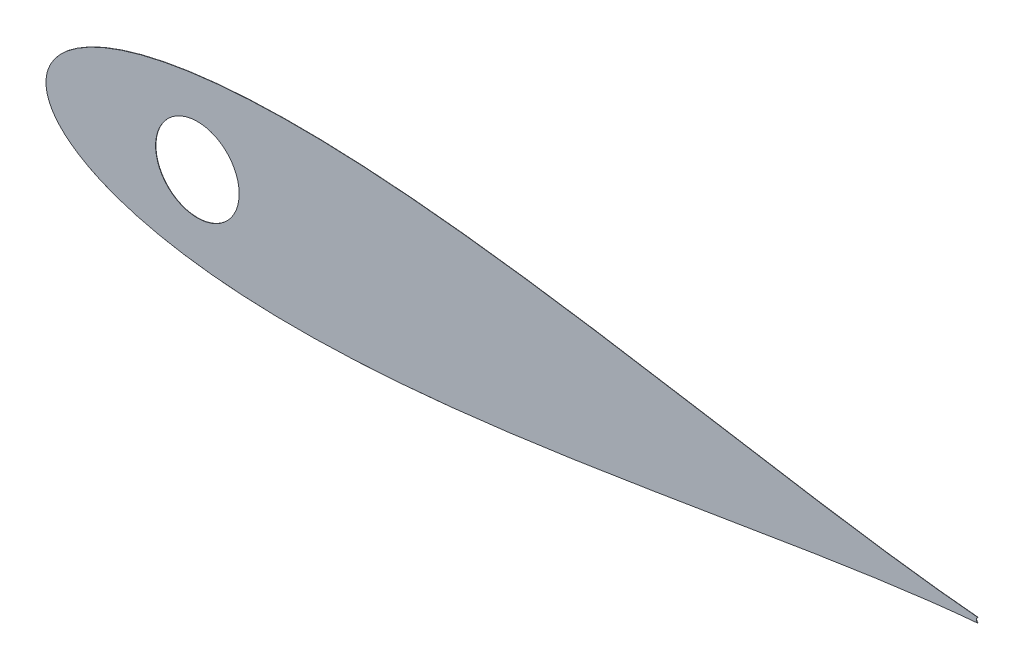
SolidWorks part; units mm, degrees
material "Custom Plastic"
ref_plane "Front Plane" through (0, 0, 0) normal (0, 0, 1) x (1, 0, 0)
ref_plane "Top Plane" through (0, 0, 0) normal (0, 1, 0) x (1, 0, 0)
ref_plane "Right Plane" through (0, 0, 0) normal (1, 0, 0) x (0, 0, -1)
sketch "Model" plane through (0, 0, 0) normal (0, 0, 1) x (1, 0, 0)
  line L0 (632.1834, 567.3179) -> (632.1834, 572.0669)
  line L1 (632.6583, 567.3179) -> (632.1834, 567.3179)
  line L2 (632.6583, 572.6096) -> (632.6583, 567.3179)
  line L3 (631.6799, 572.6096) -> (632.6583, 572.6096)
  line L4 (631.3693, 572.0669) -> (631.6799, 572.6096)
  line L5 (632.1834, 572.0669) -> (631.3693, 572.0669)
  line L6 (629.6733, 570.71) -> (628.7595, 570.71)
  line L7 (629.6733, 571.0492) -> (629.6733, 570.71)
  line L8 (628.8104, 571.0492) -> (629.6733, 571.0492)
  line L9 (629.0648, 572.7453) -> (628.8104, 571.0492)
  line L10 (628.6556, 572.7453) -> (629.0648, 572.7453)
  line L11 (628.4012, 571.0492) -> (628.6556, 572.7453)
  line L12 (627.3179, 571.0492) -> (628.4012, 571.0492)
  line L13 (627.5723, 572.7453) -> (627.3179, 571.0492)
  line L14 (627.1631, 572.7453) -> (627.5723, 572.7453)
  line L15 (626.9087, 571.0492) -> (627.1631, 572.7453)
  line L16 (625.8741, 571.0492) -> (626.9087, 571.0492)
  line L17 (625.8741, 570.71) -> (625.8741, 571.0492)
  line L18 (626.8578, 570.71) -> (625.8741, 570.71)
  line L19 (626.6744, 569.4889) -> (626.8578, 570.71)
  line L20 (625.7384, 569.4889) -> (626.6744, 569.4889)
  line L21 (625.7384, 569.1497) -> (625.7384, 569.4889)
  line L22 (626.6236, 569.1497) -> (625.7384, 569.1497)
  line L23 (626.349, 567.3179) -> (626.6236, 569.1497)
  line L24 (626.7592, 567.3179) -> (626.349, 567.3179)
  line L25 (627.0338, 569.1497) -> (626.7592, 567.3179)
  line L26 (628.1161, 569.1497) -> (627.0338, 569.1497)
  line L27 (627.8415, 567.3179) -> (628.1161, 569.1497)
  line L28 (628.2518, 567.3179) -> (627.8415, 567.3179)
  line L29 (628.5263, 569.1497) -> (628.2518, 567.3179)
  line L30 (629.5376, 569.1497) -> (628.5263, 569.1497)
  line L31 (629.5376, 569.4889) -> (629.5376, 569.1497)
  line L32 (628.5772, 569.4889) -> (629.5376, 569.4889)
  line L33 (628.7595, 570.71) -> (628.5772, 569.4889)
  line L34 (627.267, 570.71) -> (627.0847, 569.4889)
  line L35 (628.3503, 570.71) -> (627.267, 570.71)
  line L36 (628.167, 569.4889) -> (628.3503, 570.71)
  line L37 (627.0847, 569.4889) -> (628.167, 569.4889)
  arc A0 (733.0945, 571.1452) -> (733.0926, 569.082) centre (733.7898, 570.113) ccw
  circle A1 centre (374.0091, 570.113) radius 10.1301
  circle A2 centre (607.3416, 570.113) radius 6.35
  circle A3 centre (567.9716, 570.113) radius 12.7
  circle A4 centre (518.2881, 570.113) radius 19.3008
  circle A5 centre (464.3241, 570.113) radius 23.3784
  circle A6 centre (410.4916, 570.1137) radius 17.272
  spline S0 degree 3 poles (733.0945, 571.1452) (731.0717, 571.3179) (726.7738, 571.7153) (719.931, 572.4271) (712.3349, 573.3017) (704.0224, 574.3433) (695.0324, 575.5531) (685.4036, 576.9284) (675.1779, 578.462) (664.3986, 580.143) (653.1109, 581.9565) (641.3614, 583.8836) (629.1982, 585.9022) (616.6704, 587.9868) (603.8283, 590.1092) (590.7233, 592.2384) (577.4078, 594.342) (563.9349, 596.3855) (550.3591, 598.3339) (536.7354, 600.1516) (523.1201, 601.8031) (509.5703, 603.2536) (496.1441, 604.4696) (482.9006, 605.4195) (469.9, 606.074) (457.2032, 606.4066) (444.8723, 606.3942) (432.9703, 606.0174) (421.5609, 605.2612) (410.7094, 604.1149) (400.482, 602.5731) (390.9469, 600.6353) (382.1748, 598.3081) (374.2396, 595.6051) (367.2206, 592.5504) (361.2031, 589.1843) (356.2769, 585.5753) (352.525, 581.8411) (349.9848, 578.1793) (348.5684, 574.8757) (347.9964, 572.2255) (347.8662, 570.1137) (347.9964, 568.0019) (348.5684, 565.3517) (349.9848, 562.0481) (352.525, 558.3863) (356.2769, 554.6521) (361.2031, 551.0431) (367.2206, 547.677) (374.2396, 544.6223) (382.1748, 541.9193) (390.9469, 539.5921) (400.482, 537.6543) (410.7094, 536.1125) (421.5609, 534.9662) (432.9703, 534.21) (444.8723, 533.8332) (457.2032, 533.8208) (469.9, 534.1534) (482.9006, 534.8078) (496.1441, 535.7578) (509.5703, 536.9738) (523.1201, 538.4243) (536.7354, 540.0758) (550.3591, 541.8935) (563.9349, 543.8419) (577.4078, 545.8854) (590.7233, 547.989) (603.8283, 550.1182) (616.6704, 552.2406) (629.1982, 554.3252) (641.3614, 556.3438) (653.1109, 558.2709) (664.3986, 560.0844) (675.1779, 561.7654) (685.4036, 563.299) (695.0324, 564.6743) (704.0224, 565.8841) (712.3349, 566.9257) (719.931, 567.8003) (726.7732, 568.5121) (731.0705, 568.9094) (733.0926, 569.082) knots 0.021301 0.021301 0.021301 0.021301 0.028553 0.036781 0.04592 0.055932 0.066773 0.078397 0.090755 0.103793 0.117456 0.131686 0.146422 0.1616 0.177156 0.193024 0.209135 0.225421 0.241812 0.258238 0.274629 0.290914 0.307025 0.322893 0.338448 0.353626 0.368361 0.38259 0.396253 0.40929 0.421647 0.43327 0.444109 0.454119 0.463255 0.471479 0.478755 0.485052 0.490344 0.49461 0.497833 0.5 0.502167 0.50539 0.509656 0.514948 0.521245 0.528521 0.536745 0.545881 0.555891 0.56673 0.578353 0.59071 0.603747 0.61741 0.631639 0.646374 0.661552 0.677107 0.692975 0.709086 0.725371 0.741762 0.758188 0.774579 0.790865 0.806976 0.822844 0.8384 0.853578 0.868314 0.882544 0.896207 0.909245 0.921603 0.933227 0.944068 0.95408 0.963219 0.971447 0.978697 0.978697 0.978697 0.978697
  spline S1 degree 3 poles (638.2213, 569.9616) (638.2203, 569.8807) (638.2184, 569.723) (638.2085, 569.4924) (638.1889, 569.2747) (638.1644, 569.0694) (638.1304, 568.8773) (638.0887, 568.6978) (638.0424, 568.53) (637.9852, 568.3754) (637.9226, 568.2319) (637.8544, 568.0978) (637.7815, 567.9721) (637.7019, 567.8557) (637.6172, 567.7478) (637.5254, 567.6502) (637.4291, 567.5608) (637.3272, 567.4812) (637.2208, 567.4115) (637.112, 567.3492) (636.9989, 567.2989) (636.8841, 567.2558) (636.766, 567.2228) (636.6447, 567.2001) (636.5208, 567.1841) (636.437, 567.1829) (636.3949, 567.1822) knots 0 0 0 0 0.065063 0.126773 0.185516 0.240765 0.29298 0.34225 0.388919 0.432776 0.474628 0.514775 0.553606 0.591426 0.628028 0.663804 0.698984 0.733591 0.767628 0.801208 0.834264 0.866981 0.89972 0.932702 0.966176 1 1 1 1
  spline S2 degree 3 poles (636.3949, 572.7453) (636.437, 572.7445) (636.5207, 572.7431) (636.6444, 572.729) (636.7653, 572.7056) (636.8828, 572.6724) (636.9979, 572.6313) (637.1097, 572.5798) (637.2188, 572.5198) (637.3237, 572.4493) (637.4253, 572.3707) (637.5212, 572.2819) (637.6115, 572.1837) (637.6971, 572.0772) (637.7758, 571.9603) (637.8508, 571.8352) (637.9179, 571.6995) (637.9825, 571.5556) (638.0383, 571.3995) (638.0886, 571.232) (638.1292, 571.0512) (638.163, 570.8581) (638.1893, 570.6518) (638.2084, 570.433) (638.2185, 570.2013) (638.2204, 570.0429) (638.2213, 569.9616) knots 0 0 0 0 0.033788 0.067194 0.099862 0.132567 0.165151 0.197913 0.231319 0.265083 0.299255 0.334399 0.369943 0.406284 0.444064 0.482998 0.523354 0.565537 0.609613 0.656391 0.705885 0.758325 0.813832 0.872795 0.934722 1 1 1 1
  spline S3 degree 3 poles (634.6257, 569.9616) (634.6262, 570.0465) (634.6272, 570.2112) (634.6379, 570.4513) (634.6557, 570.6765) (634.6801, 570.8869) (634.7098, 571.0824) (634.7494, 571.2627) (634.7945, 571.4285) (634.8467, 571.5804) (634.9057, 571.7203) (634.9698, 571.851) (635.0417, 571.9722) (635.1173, 572.0858) (635.1996, 572.1899) (635.2862, 572.2862) (635.3806, 572.3722) (635.4795, 572.4506) (635.5838, 572.5193) (635.6906, 572.5798) (635.8006, 572.6315) (635.9141, 572.6722) (636.0301, 572.7058) (636.149, 572.7287) (636.2709, 572.7432) (636.3532, 572.7446) (636.3949, 572.7453) knots 0 0 0 0 0.068595 0.133246 0.194313 0.251279 0.304513 0.354235 0.400481 0.443411 0.484015 0.523252 0.561042 0.5979 0.633518 0.668314 0.702496 0.736685 0.770293 0.803437 0.835913 0.86846 0.900847 0.933467 0.966258 1 1 1 1
  spline S4 degree 3 poles (636.3949, 567.1822) (636.3532, 567.1829) (636.2709, 567.1843) (636.1489, 567.1987) (636.0306, 567.2218) (635.9152, 567.2542) (635.8023, 567.2939) (635.6933, 567.3455) (635.587, 567.405) (635.4838, 567.4727) (635.3855, 567.5503) (635.2916, 567.6361) (635.2045, 567.7323) (635.1234, 567.8373) (635.0463, 567.9503) (634.9754, 568.0726) (634.9098, 568.2039) (634.8499, 568.345) (634.7968, 568.498) (634.7498, 568.6645) (634.7127, 568.8461) (634.681, 569.0413) (634.6554, 569.251) (634.638, 569.4752) (634.6272, 569.7138) (634.6262, 569.8775) (634.6257, 569.9616) knots 0 0 0 0 0.033787 0.066622 0.099285 0.131361 0.163585 0.196104 0.228902 0.262158 0.295991 0.330218 0.36506 0.400951 0.43762 0.475708 0.515381 0.556414 0.599765 0.646424 0.696431 0.749782 0.806573 0.867436 0.931887 1 1 1 1
  spline S5 degree 3 poles (637.5461, 568.6334) (637.562, 568.6806) (637.5944, 568.7765) (637.6362, 568.9252) (637.6691, 569.0813) (637.6986, 569.2437) (637.7188, 569.4137) (637.7351, 569.5907) (637.7447, 569.775) (637.7458, 569.9001) (637.7464, 569.9638) knots 0 0 0 0 0.110588 0.224542 0.342503 0.464324 0.590756 0.722227 0.858843 1 1 1 1
  spline S6 degree 3 poles (636.4108, 572.2025) (636.3523, 572.1995) (636.2351, 572.1933) (636.0621, 572.1499) (635.8962, 572.0743) (635.7643, 571.9912) (635.6632, 571.9121) (635.592, 571.8435) (635.5253, 571.7684) (635.4638, 571.6862) (635.4062, 571.5978) (635.3533, 571.5026) (635.3057, 571.4) (635.2617, 571.2902) (635.223, 571.1699) (635.1912, 571.0372) (635.1617, 570.8914) (635.1408, 570.7315) (635.1223, 570.5587) (635.1104, 570.3723) (635.1011, 570.1727) (635.1008, 570.0348) (635.1006, 569.9638) knots 0 0 0 0 0.060387 0.120883 0.182755 0.247811 0.281299 0.315088 0.349702 0.384857 0.420966 0.458511 0.497175 0.537602 0.580503 0.627468 0.678388 0.733983 0.793747 0.857714 0.926698 1 1 1 1
  spline S7 degree 3 poles (636.4108, 567.725) (636.4694, 567.7274) (636.5865, 567.7322) (636.7575, 567.7788) (636.9236, 567.849) (637.0537, 567.9321) (637.1527, 568.0112) (637.2236, 568.0787) (637.2888, 568.1542) (637.3505, 568.2357) (637.4071, 568.3247) (637.4586, 568.4208) (637.5056, 568.5243) (637.5324, 568.5965) (637.5461, 568.6334) knots 0 0 0 0 0.112813 0.225394 0.339595 0.459675 0.521735 0.583926 0.648174 0.713881 0.781004 0.851451 0.924051 1 1 1 1
  spline S8 degree 3 poles (635.1006, 569.9638) (635.1008, 569.8931) (635.1011, 569.7559) (635.1103, 569.5566) (635.1228, 569.3706) (635.1389, 569.1979) (635.1628, 569.0389) (635.1895, 568.8926) (635.2221, 568.7598) (635.2606, 568.6394) (635.3046, 568.5296) (635.3525, 568.4274) (635.404, 568.3316) (635.4616, 568.2431) (635.5244, 568.1616) (635.5909, 568.0857) (635.6635, 568.0179) (635.7641, 567.9367) (635.8968, 567.8528) (636.0641, 567.7797) (636.2359, 567.7337) (636.3526, 567.7279) (636.4108, 567.725) knots 0 0 0 0 0.072951 0.141584 0.205926 0.265301 0.320597 0.371817 0.41879 0.461699 0.502134 0.540804 0.578181 0.614297 0.649678 0.684299 0.718359 0.752081 0.817652 0.879722 0.939966 1 1 1 1
  spline S9 degree 3 poles (637.7464, 569.9638) (637.7456, 570.0274) (637.744, 570.1518) (637.7378, 570.334) (637.7217, 570.5071) (637.7039, 570.6717) (637.6776, 570.8271) (637.6492, 570.9744) (637.6111, 571.1119) (637.5704, 571.2417) (637.5238, 571.3624) (637.4725, 571.4744) (637.4178, 571.5784) (637.3583, 571.6741) (637.2948, 571.7618) (637.2256, 571.8399) (637.1535, 571.9107) (637.0525, 571.9915) (636.9202, 572.0739) (636.7557, 572.1498) (636.5844, 572.1933) (636.4686, 572.1995) (636.4108, 572.2025) knots 0 0 0 0 0.065681 0.128486 0.188175 0.245106 0.299448 0.350823 0.399942 0.446672 0.491255 0.533376 0.573853 0.612526 0.649597 0.685532 0.720106 0.753838 0.818925 0.880493 0.940311 1 1 1 1
sketch "Sketch2" plane through (0, 0, 0) normal (0, 0, 1) x (1, 0, 0)
  arc A0 (733.0945, 571.1452) -> (733.0926, 569.082) centre (733.7898, 570.113) ccw
  circle A6 centre (410.4916, 570.1137) radius 17.272
  spline S0 degree 3 poles (733.0945, 571.1452) (731.0717, 571.3179) (726.7738, 571.7153) (719.931, 572.4271) (712.3349, 573.3017) (704.0224, 574.3433) (695.0324, 575.5531) (685.4036, 576.9284) (675.1779, 578.462) (664.3986, 580.143) (653.1109, 581.9565) (641.3614, 583.8836) (629.1982, 585.9022) (616.6704, 587.9868) (603.8283, 590.1092) (590.7233, 592.2384) (577.4078, 594.342) (563.9349, 596.3855) (550.3591, 598.3339) (536.7354, 600.1516) (523.1201, 601.8031) (509.5703, 603.2536) (496.1441, 604.4696) (482.9006, 605.4195) (469.9, 606.074) (457.2032, 606.4066) (444.8723, 606.3942) (432.9703, 606.0174) (421.5609, 605.2612) (410.7094, 604.1149) (400.482, 602.5731) (390.9469, 600.6353) (382.1748, 598.3081) (374.2396, 595.6051) (367.2206, 592.5504) (361.2031, 589.1843) (356.2769, 585.5753) (352.525, 581.8411) (349.9848, 578.1793) (348.5684, 574.8757) (347.9964, 572.2255) (347.8662, 570.1137) (347.9964, 568.0019) (348.5684, 565.3517) (349.9848, 562.0481) (352.525, 558.3863) (356.2769, 554.6521) (361.2031, 551.0431) (367.2206, 547.677) (374.2396, 544.6223) (382.1748, 541.9193) (390.9469, 539.5921) (400.482, 537.6543) (410.7094, 536.1125) (421.5609, 534.9662) (432.9703, 534.21) (444.8723, 533.8332) (457.2032, 533.8208) (469.9, 534.1534) (482.9006, 534.8078) (496.1441, 535.7578) (509.5703, 536.9738) (523.1201, 538.4243) (536.7354, 540.0758) (550.3591, 541.8935) (563.9349, 543.8419) (577.4078, 545.8854) (590.7233, 547.989) (603.8283, 550.1182) (616.6704, 552.2406) (629.1982, 554.3252) (641.3614, 556.3438) (653.1109, 558.2709) (664.3986, 560.0844) (675.1779, 561.7654) (685.4036, 563.299) (695.0324, 564.6743) (704.0224, 565.8841) (712.3349, 566.9257) (719.931, 567.8003) (726.7732, 568.5121) (731.0705, 568.9094) (733.0926, 569.082) knots 0.021301 0.021301 0.021301 0.021301 0.028553 0.036781 0.04592 0.055932 0.066773 0.078397 0.090755 0.103793 0.117456 0.131686 0.146422 0.1616 0.177156 0.193024 0.209135 0.225421 0.241812 0.258238 0.274629 0.290914 0.307025 0.322893 0.338448 0.353626 0.368361 0.38259 0.396253 0.40929 0.421647 0.43327 0.444109 0.454119 0.463255 0.471479 0.478755 0.485052 0.490344 0.49461 0.497833 0.5 0.502167 0.50539 0.509656 0.514948 0.521245 0.528521 0.536745 0.545881 0.555891 0.56673 0.578353 0.59071 0.603747 0.61741 0.631639 0.646374 0.661552 0.677107 0.692975 0.709086 0.725371 0.741762 0.758188 0.774579 0.790865 0.806976 0.822844 0.8384 0.853578 0.868314 0.882544 0.896207 0.909245 0.921603 0.933227 0.944068 0.95408 0.963219 0.971447 0.978697 0.978697 0.978697 0.978697
extrude "Boss-Extrude1" add sketch "Sketch2" along normal blind 0.127
